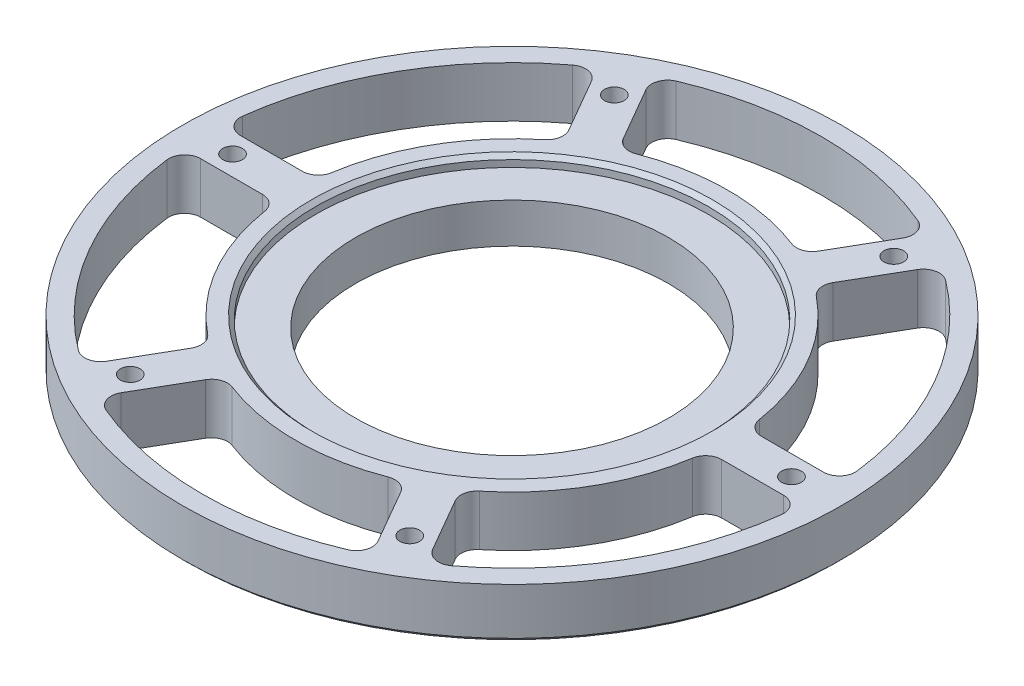
SolidWorks part; units mm, degrees
material "6061-T6 (SS)"
ref_plane "Front Plane" through (0, 0, 0) normal (0, 0, 1) x (1, 0, 0)
ref_plane "Top Plane" through (0, 0, 0) normal (0, 1, 0) x (1, 0, 0)
ref_plane "Right Plane" through (0, 0, 0) normal (1, 0, 0) x (0, 0, -1)
sketch "Sketch2" plane through (0, 0, 0) normal (1, 0, 0) x (0, 0, -1)
  line L0 (-39.2125, 0) -> (-82.55, 0)
  line L1 (-82.55, 0) -> (-82.55, 12.7)
  line L2 (-82.55, 12.7) -> (-49.2125, 12.7)
  line L3 (-49.2125, 12.7) -> (-49.2125, 10)
  line L4 (-49.2125, 10) -> (-39.2125, 10)
  line L5 (-39.2125, 10) -> (-39.2125, 0)
  dimension "D1" = 82.55
  dimension "D2" = 12.7
  dimension "D4" = 49.2125
  dimension "D5" = 10
  dimension "D3" = 10
ref_axis "Axis1" through (0, -0.635, 0) along (0, 1, 0)
revolve "Revolve1" add sketch "Sketch2" angle 360 about axis through (0, -0.635, 0) along (0, 1, 0)
hole_wizard "#10 (0.1935) Diameter Hole1" positions "Sketch6" profile "Sketch7" hole size "#10" standard "ANSI Inch" end condition through all
sketch "Sketch6" plane through (0, 12.7, 0) normal (0, 1, 0) x (1, 0, 0)
  line L0 (0, 0) -> (-69.8201, 120.932) construction
  line L2 (0, 0) -> (0, 109.0908) construction
  point P0 (-35, 60.6218)
  dimension "D1" = 30
  dimension "D2" = 70
sketch "Sketch7" plane through (-35, 12.7, -60.6218) normal (1, 0, 0) x (0, 0, 1)
  line L0 (0, 0) -> (0, 12.7)
  line L1 (0, 12.7) -> (2.4574, 12.7)
  line L2 (2.4574, 12.7) -> (2.4574, 0)
  line L5 (2.4574, 0) -> (0, 0)
  line L11 (0, -6.35) -> (0, 107.95) construction
  dimension "Thru Hole Dia." = 4.9149
  dimension "Thru Hole Depth" = 12.7
pattern_circular "CirPattern3" count 6 over 360 about axis through (0, 0, 0) along (0, 1, 0) of "#10 (0.1935) Diameter Hole1"
sketch "Sketch8" plane through (0, 12.7, 0) normal (0, 1, 0) x (1, 0, 0)
  line L0 (-34.3642, 69.5205) -> (-22.6606, 49.2493)
  line L1 (34.3642, 69.5205) -> (22.6606, 49.2493)
  line L2 (0, 0) -> (-35, 60.6218) construction
  line L4 (0, 0) -> (0, 93.9995) construction
  arc A0 (-22.6606, 49.2493) -> (22.6606, 49.2493) centre (0, 0) cw
  arc A1 (-34.3642, 69.5205) -> (34.3642, 69.5205) centre (0, 0) cw
  circle A2 centre (0, 0) radius 49.2125 construction
  circle A3 centre (0, 0) radius 82.55 construction
  dimension "D1" = 5
  dimension "D2" = 5
  dimension "D3" = 5
extrude "Cut-Extrude1" cut sketch "Sketch8" against normal through all
fillet "Fillet1" radius 4 4 edges at (34.3642, 6.35, -69.5205) (22.6606, 6.35, -49.2493) (-34.3642, 6.35, -69.5205) (-22.6606, 6.35, -49.2493)
pattern_circular "CirPattern4" count 6 over 360 about axis through (0, 0, 0) along (0, 1, 0) of "Cut-Extrude1", "Fillet1"
chamfer "Chamfer1" distance 1 angle 45 1 edges at (0, 12.7, -49.2125)
chamfer "Chamfer2" distance 1 angle 45 1 edges at (0, 0, -82.55)
equation "\"TubeDiameter\"= 6.500in"
equation "\"D1@Sketch2\"=\"TubeDiameter\"/2"
